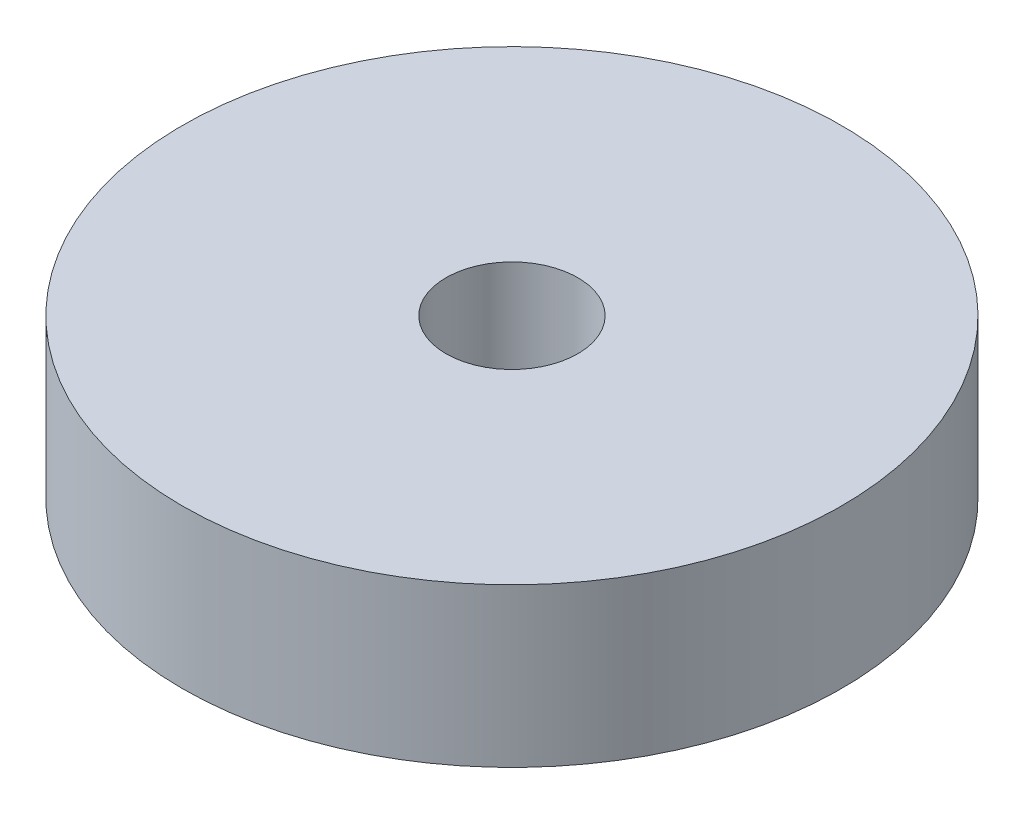
SolidWorks part; units mm, degrees
material "AISI 1035 钢 (SS)"
ref_plane "前视基准面" through (0, 0, 0) normal (0, 0, 1) x (1, 0, 0)
ref_plane "上视基准面" through (0, 0, 0) normal (0, 1, 0) x (1, 0, 0)
ref_plane "右视基准面" through (0, 0, 0) normal (1, 0, 0) x (0, 0, -1)
sketch "草图1" plane through (0, 0, 0) normal (0, 1, 0) x (1, 0, 0)
  circle A0 centre (0, 0) radius 2.5
  circle A1 centre (0, 0) radius 12.5
  dimension "D1" = 5
  dimension "D2" = 25
extrude "凸台-拉伸1" add sketch "草图1" along normal blind 6
